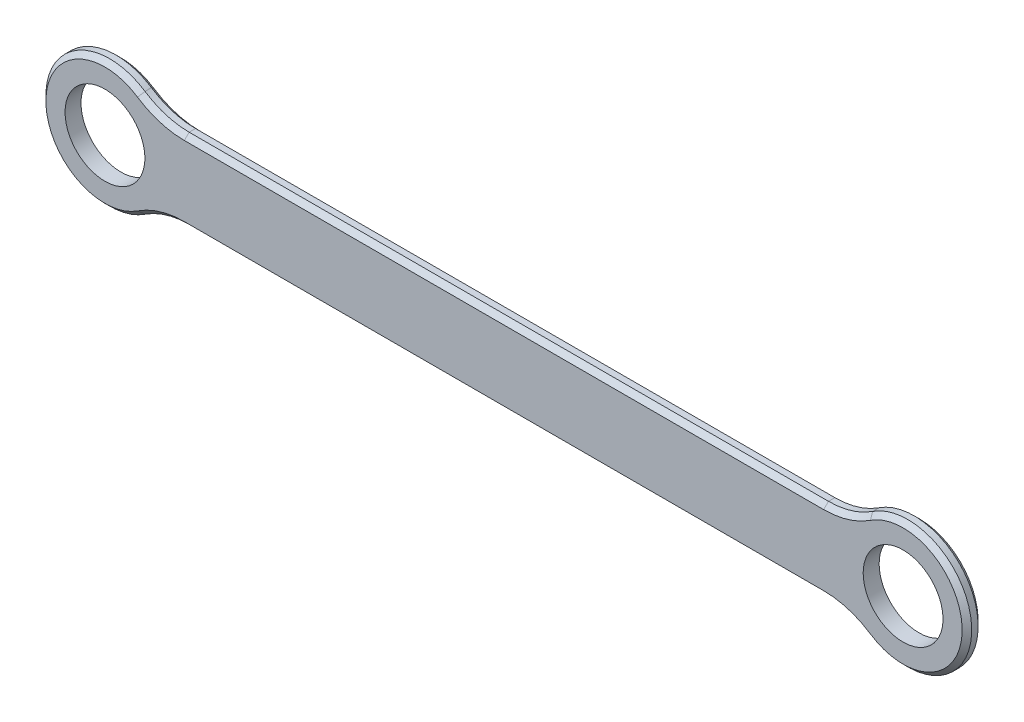
SolidWorks part; units mm, degrees
ref_plane "Front Plane" through (0, 0, 0) normal (0, 0, 1) x (1, 0, 0)
ref_plane "Top Plane" through (0, 0, 0) normal (0, 1, 0) x (1, 0, 0)
ref_plane "Right Plane" through (0, 0, 0) normal (1, 0, 0) x (0, 0, -1)
sketch "Sketch2" plane through (0, 0, 0) normal (0, 0, 1) x (1, 0, 0)
  line L5 (-2.2134, -0.4577) -> (2.1621, -0.4577)
  line L6 (-2.2134, 0.0423) -> (2.1621, 0.0423)
  line L7 (2.4744, -0.2077) -> (2.8744, -0.2077) construction
  circle A0 centre (-2.5256, -0.2077) radius 0.25
  circle A1 centre (2.4744, -0.2077) radius 0.25
  circle A2 centre (-2.5256, -0.2077) radius 0.4
  circle A3 centre (2.4744, -0.2077) radius 0.4
  point P0 (0, 0)
extrude "Boss-Extrude1" add sketch "Sketch2" along normal blind 0.1 contours A3 L6 A2 L5
fillet "Fillet1" radius 0.5 1 edges at (2.1621, 0.0423, 0.05)
fillet "Fillet2" radius 0.5 3 edges at (-2.2134, 0.0423, 0.05) (-2.2134, -0.4577, 0.05) (2.1621, -0.4577, 0.05)
chamfer "Chamfer2" distance 0.03 angle 45 8 edges at (-2.1725, 0.0636, 0.1) (-0.0256, 0.0423, 0.1) (2.1212, 0.0636, 0.1) (2.8744, -0.2077, 0.1) (2.1212, -0.479, 0.1) (-0.0256, -0.4577, 0.1) (-2.1725, -0.479, 0.1) (-2.9256, -0.2077, 0.1)
chamfer "Chamfer3" distance 0.03 angle 45 8 edges at (-2.1725, -0.479, 0) (-0.0256, -0.4577, 0) (2.1212, -0.479, 0) (2.8744, -0.2077, 0) (2.1212, 0.0636, 0) (-0.0256, 0.0423, 0) (-2.1725, 0.0636, 0) (-2.9256, -0.2077, 0)
sketch "Sketch3" plane through (0, 0, 0) normal (0, 0, -1) x (-1, 0, 0)
  circle A0 centre (-2.4744, -0.2077) radius 0.25
  circle A1 centre (2.5256, -0.2077) radius 0.25
  dimension "D1" = 0.5
  dimension "D2" = 0.5
extrude "Cut-Extrude1" cut sketch "Sketch3" against normal through all both and the other way through all contours A0 | A1
